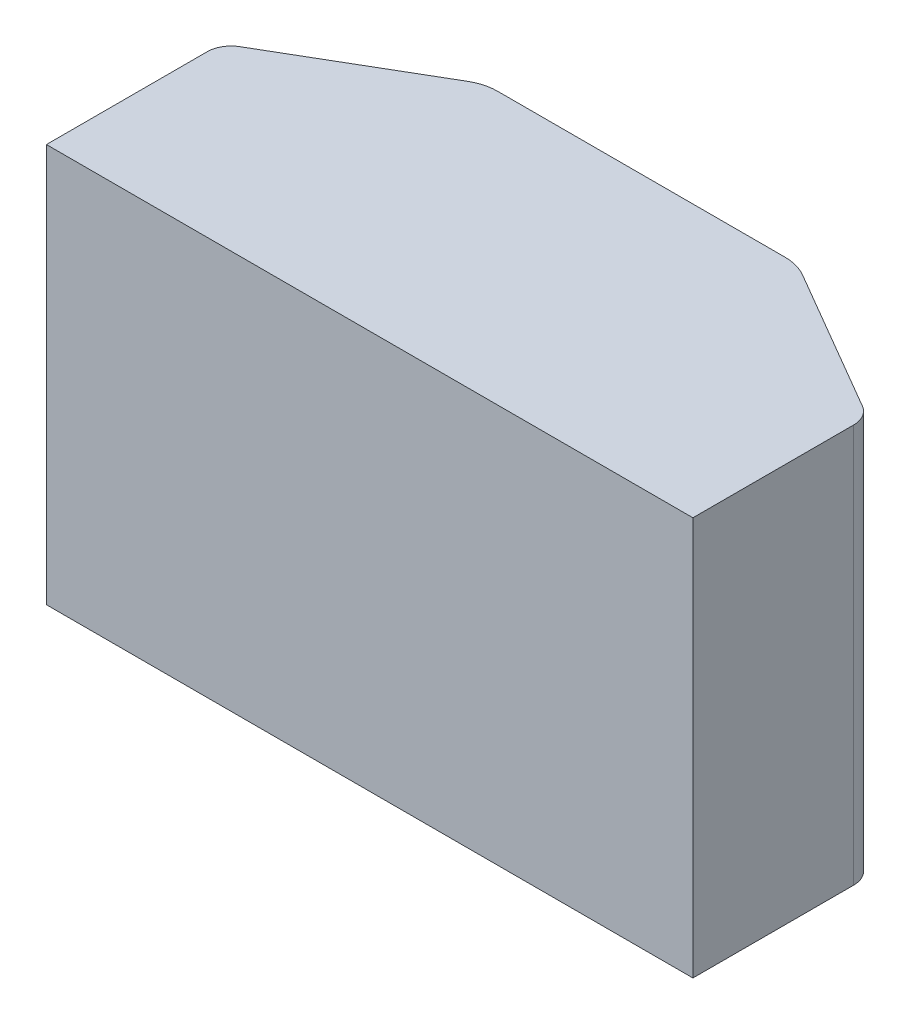
SolidWorks part; units mm, degrees
ref_plane "Front Plane" through (0, 0, 0) normal (0, 0, 1) x (1, 0, 0)
ref_plane "Top Plane" through (0, 0, 0) normal (0, 1, 0) x (1, 0, 0)
ref_plane "Right Plane" through (0, 0, 0) normal (1, 0, 0) x (0, 0, -1)
sketch "Sketch1" plane through (0, 0, 0) normal (0, 0, 1) x (1, 0, 0)
  line L1 (0, 0) -> (135.6, 0)
  line L2 (0, 0) -> (0, -83.6)
  line L3 (0, -83.6) -> (135.6, -83.6)
  line L4 (135.6, 0) -> (135.6, -83.6)
  dimension "D1" = 135.6
  dimension "D2" = 83.6
extrude "Boss-Extrude1" add sketch "Sketch1" along normal blind 57
sketch "Sketch3" plane through (0, 0, 0) normal (0, 1, 0) x (1, 0, 0)
  line L0 (100.6, 0) -> (135.6, 0)
  line L1 (135.6, -57) -> (0, -57) construction
  line L3 (135.6, 0) -> (135.6, -20.4)
  line L4 (135.6, 0) -> (0, 0) construction
  line L5 (100.6, 0) -> (135.6, -20.4)
  line L6 (67.8, 0) -> (67.8, -60.8644) construction
  line L7 (35, 0) -> (0, 0)
  line L8 (35, 0) -> (0, -20.4)
  line L9 (0, 0) -> (0, -20.4)
  dimension "D1" = 40.5112
  dimension "D2" = 36.6
extrude "Cut-Extrude2" cut sketch "Sketch3" against normal through all
fillet "Fillet2" radius 10 2 edges at (100.6, -41.8, 0) (35, -41.8, 0)
fillet "Fillet3" radius 5 2 edges at (135.6, -41.8, 20.4) (0, -41.8, 20.4)
